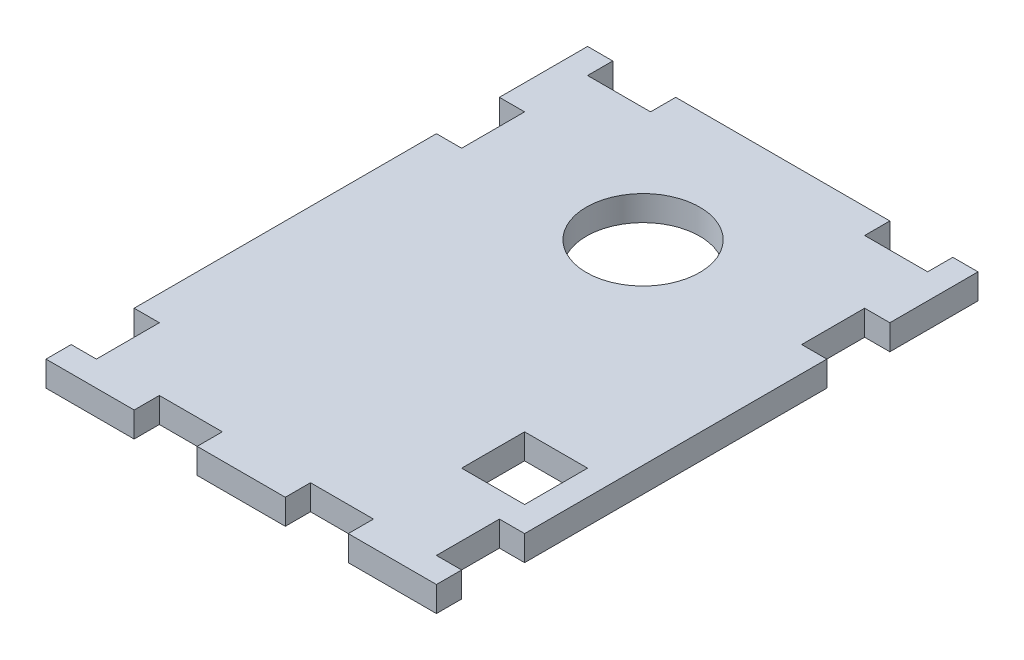
SolidWorks part; units mm, degrees
ref_plane "Front Plane" through (0, 0, 0) normal (0, 0, 1) x (1, 0, 0)
ref_plane "Top Plane" through (0, 0, 0) normal (0, 1, 0) x (1, 0, 0)
ref_plane "Right Plane" through (0, 0, 0) normal (1, 0, 0) x (0, 0, -1)
sketch "Sketch1" plane through (0, 0, 0) normal (0, 1, 0) x (1, 0, 0)
  line L1 (15.5, -21.5) -> (-15.5, -21.5)
  line L2 (15.5, -21.5) -> (15.5, 21.5)
  line L3 (15.5, 21.5) -> (-15.5, 21.5)
  line L4 (-15.5, -21.5) -> (-15.5, 21.5)
  line L5 (15.5, -21.5) -> (-15.5, 21.5) construction
  line L6 (15.5, 21.5) -> (-15.5, -21.5) construction
  point P0 (0, 0)
  dimension "D1" = 31
  dimension "D2" = 43
extrude "Boss-Extrude1" add sketch "Sketch1" along normal blind 2
sketch "Sketch2" plane through (0, 2, 0) normal (0, 1, 0) x (1, 0, 0)
  line L0 (-15.5, 19.5) -> (-13.5, 19.5)
  line L1 (-15.5, 21.5) -> (-15.5, -21.5) construction
  line L2 (15.5, 21.5) -> (-15.5, 21.5) construction
  line L3 (-13.5, 19.5) -> (-8.5, 19.5)
  line L4 (-13.5, 19.5) -> (-13.5, 21.5)
  line L5 (-13.5, 21.5) -> (-8.5, 21.5)
  line L6 (-8.5, 19.5) -> (-8.5, 21.5)
  line L7 (15.5, 19.5) -> (13.5, 19.5)
  line L8 (15.5, -21.5) -> (15.5, 21.5) construction
  line L10 (13.5, 19.5) -> (8.5, 19.5)
  line L11 (13.5, 19.5) -> (13.5, 21.5)
  line L12 (13.5, 21.5) -> (8.5, 21.5)
  line L13 (8.5, 19.5) -> (8.5, 21.5)
  line M9 (15.5, 21.5) -> (-15.5, 21.5)
  dimension "D1" = 2
  dimension "D2" = 5
  dimension "D3" = 2
  dimension "D4" = 2
  dimension "D5" = 5
extrude "Cut-Extrude1" cut sketch "Sketch2" against normal blind 2 contours L13 L10 L11 M9 | L4 L5 L6 L3
sketch "Sketch3" plane through (0, 2, 0) normal (0, 1, 0) x (1, 0, 0)
  line L0 (-15.5, 21.5) -> (-15.5, 14.5)
  line L1 (-15.5, 21.5) -> (-15.5, -21.5) construction
  line L2 (15.5, -21.5) -> (15.5, 21.5) construction
  line L3 (-15.5, 14.5) -> (-13.5, 14.5)
  line L4 (-15.5, 14.5) -> (-15.5, 9.5)
  line L5 (-15.5, 9.5) -> (-13.5, 9.5)
  line L6 (-13.5, 14.5) -> (-13.5, 9.5)
  line L7 (15.5, 14.5) -> (13.5, 14.5)
  line L8 (15.5, 14.5) -> (15.5, 9.5)
  line L9 (15.5, 9.5) -> (13.5, 9.5)
  line L10 (13.5, 14.5) -> (13.5, 9.5)
  line L11 (-15.5, -21.5) -> (-15.5, -19.5)
  line L12 (-15.5, -21.5) -> (-8.5, -21.5)
  line L13 (-15.5, -19.5) -> (-13.5, -19.5)
  line L14 (-15.5, -19.5) -> (-15.5, -14.5)
  line L15 (-15.5, -14.5) -> (-13.5, -14.5)
  line L16 (-13.5, -19.5) -> (-13.5, -14.5)
  line L17 (15.5, -19.5) -> (13.5, -19.5)
  line L18 (15.5, -19.5) -> (15.5, -14.5)
  line L19 (15.5, -14.5) -> (13.5, -14.5)
  line L20 (13.5, -19.5) -> (13.5, -14.5)
  line L21 (-15.5, -21.5) -> (15.5, -21.5) construction
  line L22 (15.5, -21.5) -> (8.5, -21.5)
  line L23 (15.5, -14.5) -> (15.5, -12.5)
  line L24 (-8.5, -21.5) -> (-3.5, -21.5)
  line L25 (-8.5, -21.5) -> (-8.5, -19.5)
  line L26 (-8.5, -19.5) -> (-3.5, -19.5)
  line L27 (-3.5, -21.5) -> (-3.5, -19.5)
  line L28 (8.5, -21.5) -> (3.5, -21.5)
  line L29 (8.5, -21.5) -> (8.5, -19.5)
  line L30 (8.5, -19.5) -> (3.5, -19.5)
  line L31 (3.5, -21.5) -> (3.5, -19.5)
  line L33 (13.5, -12.5) -> (8.5, -12.5)
  line L34 (13.5, -12.5) -> (13.5, -7.5)
  line L35 (13.5, -7.5) -> (8.5, -7.5)
  line L36 (8.5, -12.5) -> (8.5, -7.5)
  circle A0 centre (0, 10.405) radius 4.5
  line M22 (-15.5, 21.5) -> (-15.5, -21.5)
  line M23 (-15.5, -21.5) -> (15.5, -21.5)
  line M24 (15.5, -21.5) -> (15.5, 21.5)
  dimension "D1" = 7
  dimension "D2" = 2
  dimension "D3" = 5
  dimension "D4" = 2
  dimension "D5" = 2
  dimension "D6" = 5
  dimension "D7" = 7
  dimension "D8" = 7
  dimension "D9" = 5
  dimension "D10" = 5
  dimension "D11" = 2
  dimension "D12" = 5
  dimension "D13" = 5
extrude "Cut-Extrude2" cut sketch "Sketch3" against normal blind 2 contours A0 | L36 L33 L34 L35 | L20 L17 L19 M24 | L31 L29 L30 M23 | L13 L16 L15 M22 | L27 L26 L25 M23 | L10 L9 L8 L7 | L4 L5 L6 L3
